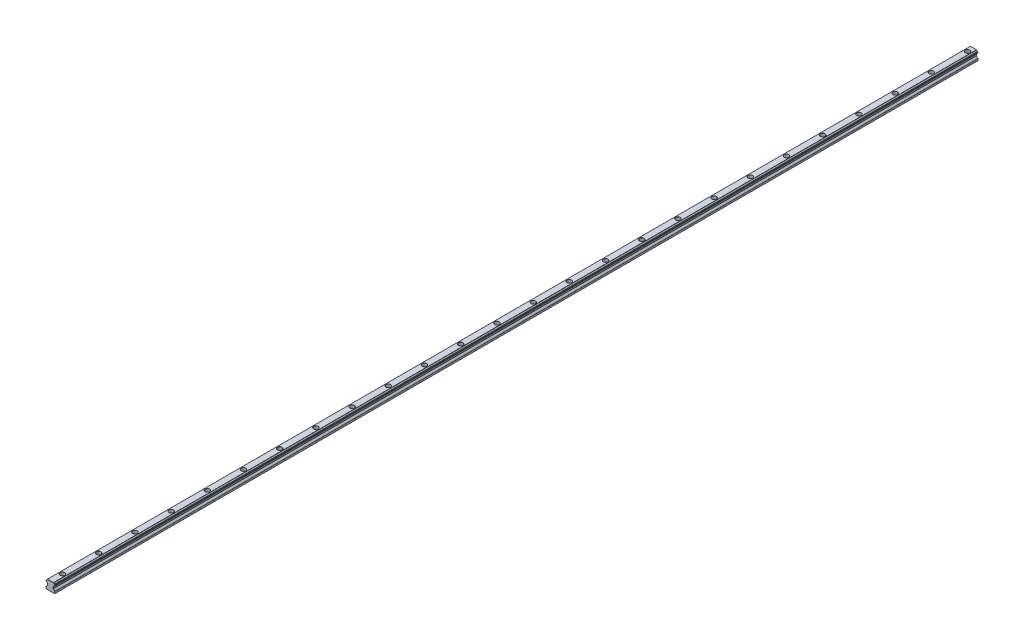
SolidWorks part; units mm, degrees
material "Plain Carbon Steel"
ref_plane "Front Plane" through (0, 0, 0) normal (0, 0, 1) x (1, 0, 0)
ref_plane "Top Plane" through (0, 0, 0) normal (0, 1, 0) x (1, 0, 0)
ref_plane "Right Plane" through (0, 0, 0) normal (1, 0, 0) x (0, 0, -1)
sketch "Rail Profile" plane through (0, 0, 0) normal (0, 0, 1) x (1, 0, 0)
  line L47 (0, 0) -> (0, 20) construction
  line L48 (-7, 0) -> (7, 0)
  line L49 (7, 0) -> (7.5, 0.5)
  line L50 (7.5, 0.5) -> (7.5, 3.0858)
  line L58 (7.2071, 3.7929) -> (4.8672, 6.1328)
  line L59 (4.75, 6.4157) -> (4.75, 8.5843)
  line L60 (4.8672, 8.8672) -> (5.063, 9.063)
  line L61 (7.5, 11.6657) -> (7.5, 12.3343)
  line L62 (-7, 0) -> (-7.5, 0.5)
  line L63 (5, 15) -> (-5, 15)
  line L64 (6.75, 9) -> (6.75, 15) construction
  line L65 (5.063, 14.937) -> (5, 15)
  line L66 (-7.5, 0.5) -> (-7.5, 3.0858)
  line L67 (6.75, 15) -> (3.75, 12) construction
  line L68 (3.75, 12) -> (6.75, 9) construction
  line L69 (7.1, 12.3343) -> (7.1, 11.6657) construction
  line L70 (6.4042, 13.0301) -> (6.4042, 10.9699) construction
  line L71 (-7.2071, 3.7929) -> (-4.8672, 6.1328)
  line L72 (-4.75, 6.4157) -> (-4.75, 8.5843)
  line L73 (-4.8672, 8.8672) -> (-5.063, 9.063)
  line L74 (5, 15) -> (8, 12) construction
  line L75 (4.8672, 8.8672) -> (8, 12) construction
  line L76 (-7.5, 11.6657) -> (-7.5, 12.3343)
  line L77 (-5.063, 14.937) -> (-5, 15)
  arc A4 (6.4734, 13.4241) -> (5.1741, 14.7234) centre (6.75, 15) cw
  arc A6 (5.1741, 9.2766) -> (6.4734, 10.5759) centre (6.75, 9) cw
  arc A7 (7.2071, 3.7929) -> (7.5, 3.0858) centre (6.5, 3.0858) cw
  arc A8 (5.063, 14.937) -> (5.1741, 14.7234) centre (4.7801, 14.6542) cw
  arc A9 (6.4734, 13.4241) -> (6.8012, 13.0792) centre (6.4042, 13.0301) cw
  arc A10 (7.1491, 12.7313) -> (7.5, 12.3343) centre (7.1, 12.3343) cw
  arc A11 (7.5, 11.6657) -> (7.1491, 11.2687) centre (7.1, 11.6657) cw
  arc A12 (6.8012, 10.9208) -> (6.4734, 10.5759) centre (6.4042, 10.9699) cw
  arc A13 (5.1741, 9.2766) -> (5.063, 9.063) centre (4.7801, 9.3458) cw
  arc A14 (4.8672, 8.8672) -> (4.75, 8.5843) centre (5.15, 8.5843) ccw
  arc A15 (4.75, 6.4157) -> (4.8672, 6.1328) centre (5.15, 6.4157) ccw
  arc A16 (6.8012, 13.0792) -> (7.1491, 12.7313) centre (7.1981, 13.1283) ccw
  arc A17 (7.1491, 11.2687) -> (6.8012, 10.9208) centre (7.1981, 10.8717) ccw
  arc A18 (-7.2071, 3.7929) -> (-7.5, 3.0858) centre (-6.5, 3.0858) ccw
  arc A19 (-4.75, 6.4157) -> (-4.8672, 6.1328) centre (-5.15, 6.4157) cw
  arc A20 (-4.8672, 8.8672) -> (-4.75, 8.5843) centre (-5.15, 8.5843) cw
  arc A21 (-5.1741, 9.2766) -> (-5.063, 9.063) centre (-4.7801, 9.3458) ccw
  arc A22 (-5.1741, 9.2766) -> (-6.4734, 10.5759) centre (-6.75, 9) ccw
  arc A23 (-6.8012, 10.9208) -> (-6.4734, 10.5759) centre (-6.4042, 10.9699) ccw
  arc A24 (-7.1491, 11.2687) -> (-6.8012, 10.9208) centre (-7.1981, 10.8717) cw
  arc A25 (-7.5, 11.6657) -> (-7.1491, 11.2687) centre (-7.1, 11.6657) ccw
  arc A26 (-7.1491, 12.7313) -> (-7.5, 12.3343) centre (-7.1, 12.3343) ccw
  arc A27 (-6.8012, 13.0792) -> (-7.1491, 12.7313) centre (-7.1981, 13.1283) cw
  arc A28 (-6.4734, 13.4241) -> (-6.8012, 13.0792) centre (-6.4042, 13.0301) ccw
  arc A29 (-6.4734, 13.4241) -> (-5.1741, 14.7234) centre (-6.75, 15) ccw
  arc A30 (-5.063, 14.937) -> (-5.1741, 14.7234) centre (-4.7801, 14.6542) ccw
  point P2 (4.75, 7.5)
  point P12 (7.5, 12)
  point P19 (6.75, 12)
  point P25 (5.1578, 14.8422)
  point P50 (8, 12)
  point P78 (0, 15)
  dimension "Rb" = 1.6
  dimension "Rf1" = 1
  dimension "Rf2" = 0.4
  dimension "WR" = 15
  dimension "Wi" = 9.5
  dimension "Wt" = 5
  dimension "Ac" = 135
  dimension "HR" = 15
  dimension "Hm" = 7.5
  dimension "Hb" = 12
  dimension "Hc" = 0.5
  dimension "Wb" = 7.5
extrude "Body" add sketch "Rail Profile" against normal blind 1530
chamfer "Aesthetic Chamfer" distance 0.15 angle 45 84 edges at (-5.0315, 14.9685, 0) (-5.135, 14.8388, 0) (-5.6186, 13.8686, 0) (-6.6941, 13.3057, 0) (-6.9153, 12.8454, 0) (-7.3997, 12.5992, 0) (-7.5, 12, 0) (-7.3997, 11.4008, 0) (-6.9153, 11.1546, 0) (-6.6941, 10.6943, 0) (-5.6186, 10.1314, 0) (-5.135, 9.1612, 0) (-4.9651, 8.9651, 0) (-4.7804, 8.7374, 0) (-4.75, 7.5, 0) (-4.7804, 6.2626, 0) (-6.0371, 4.9629, 0) (-7.4239, 3.4685, 0) (-7.5, 1.7929, 0) (-7.25, 0.25, 0) (0, 0, 0) (7.25, 0.25, 0) (5.0315, 14.9685, 0) (5.135, 14.8388, 0) (5.6186, 13.8686, 0) (6.6941, 13.3057, 0) (6.9153, 12.8454, 0) (7.3997, 12.5992, 0) (7.5, 12, 0) (7.3997, 11.4008, 0) (6.9153, 11.1546, 0) (6.6941, 10.6943, 0) (5.6186, 10.1314, 0) (5.135, 9.1612, 0) (4.9651, 8.9651, 0) (4.7804, 8.7374, 0) (7.5, 1.7929, 0) (4.75, 7.5, 0) (7.4239, 3.4685, 0) (4.7804, 6.2626, 0) (6.0371, 4.9629, 0) (0, 15, 0) (5.0315, 14.9685, -1530) (5.135, 14.8388, -1530) (5.6186, 13.8686, -1530) (6.6941, 13.3057, -1530) (6.9153, 12.8454, -1530) (7.3997, 12.5992, -1530) (7.5, 12, -1530) (7.3997, 11.4008, -1530) (6.9153, 11.1546, -1530) (6.6941, 10.6943, -1530) (5.6186, 10.1314, -1530) (5.135, 9.1612, -1530) (4.9651, 8.9651, -1530) (4.7804, 8.7374, -1530) (4.75, 7.5, -1530) (4.7804, 6.2626, -1530) (6.0371, 4.9629, -1530) (7.4239, 3.4685, -1530) (7.5, 1.7929, -1530) (7.25, 0.25, -1530) (0, 0, -1530) (-7.25, 0.25, -1530) (-5.0315, 14.9685, -1530) (-5.135, 14.8388, -1530) (-5.6186, 13.8686, -1530) (-6.6941, 13.3057, -1530) (-6.9153, 12.8454, -1530) (-7.3997, 12.5992, -1530) (-7.5, 12, -1530) (-7.3997, 11.4008, -1530) (-6.9153, 11.1546, -1530) (-6.6941, 10.6943, -1530) (-5.6186, 10.1314, -1530) (-7.5, 1.7929, -1530) (-5.135, 9.1612, -1530) (-7.4239, 3.4685, -1530) (-4.9651, 8.9651, -1530) (-6.0371, 4.9629, -1530) (-4.7804, 8.7374, -1530) (-4.7804, 6.2626, -1530) (-4.75, 7.5, -1530) (0, 15, -1530)
hole_wizard "Mounting Hole" positions "3DSketch1" profile "Sketch1" counterbore size "M4" standard "ISO" end condition through all
sketch3d "3DSketch1"
  point P0 (0, 15, -20)
  dimension "D1" = 7.5
  dimension "E1" = 20
sketch "Sketch1" plane through (0, 15, -20) normal (1, 0, 0) x (0, 0, 1)
  line L0 (0, 0) -> (0, 15)
  line L1 (2.25, 14.9) -> (2.35, 15)
  line L2 (2.25, 14.9) -> (2.25, 5.4)
  line L3 (2.25, 5.4) -> (2.35, 5.3)
  line L4 (2.35, 5.3) -> (3.75, 5.3)
  line L5 (3.75, 5.3) -> (3.75, 0.1)
  line L6 (3.75, 0.1) -> (3.85, 0)
  line L7 (3.85, 0) -> (0, 0)
  line L8 (-3.75, 0.1) -> (-3.85, 0) construction
  line L9 (-2.25, 5.4) -> (-2.35, 5.3) construction
  line L11 (0, -6.35) -> (0, 107.95) construction
  line L12 (2.35, 15) -> (0, 15)
  line L13 (-2.25, 14.9) -> (-2.35, 15) construction
  dimension "Thru Hole Dia." = 4.5
  dimension "Thru Hole Depth" = 15
  dimension "C'Bore Dia." = 7.5
  dimension "C'Bore Depth" = 5.3
  dimension "Near C'Sink Dia." = 7.7
  dimension "Near C'Sink Angle" = 90
  dimension "Mid C'Sink Dia." = 4.7
  dimension "Mid C'Sink Angle" = 90
  dimension "Far C'Sink Dia." = 4.7
  dimension "Far C'Sink Angle" = 90
fillet "Production Fillet" radius 0.1 1 edges at (0, 9.7, -16.25)
pattern_linear "Mounting Holes Pattern" count 26 spacing 60 along (0, 0, -1) of "Mounting Hole", "Production Fillet"
equation "\"Wt@Rail Profile\"= \"WR@Rail Profile\" / 3'Top Side Half Width"
equation "\"Hm@Rail Profile\"= \"HR@Rail Profile\" / 2'Recirculation Avoidance Height"
equation "\"Hb@Rail Profile\"= 0.8 * \"HR@Rail Profile\"'Pivot Height"
equation "\"Hc@Rail Profile\"= \"WR@Rail Profile\" / 30'Chamfer Width"
equation "\"Wb@Rail Profile\"= \"WR@Rail Profile\" / 2'Ball Center Cross Width"
equation "\"D1@3DSketch1\"= \"WR@Rail Profile\" / 2'Hole Center Position"
